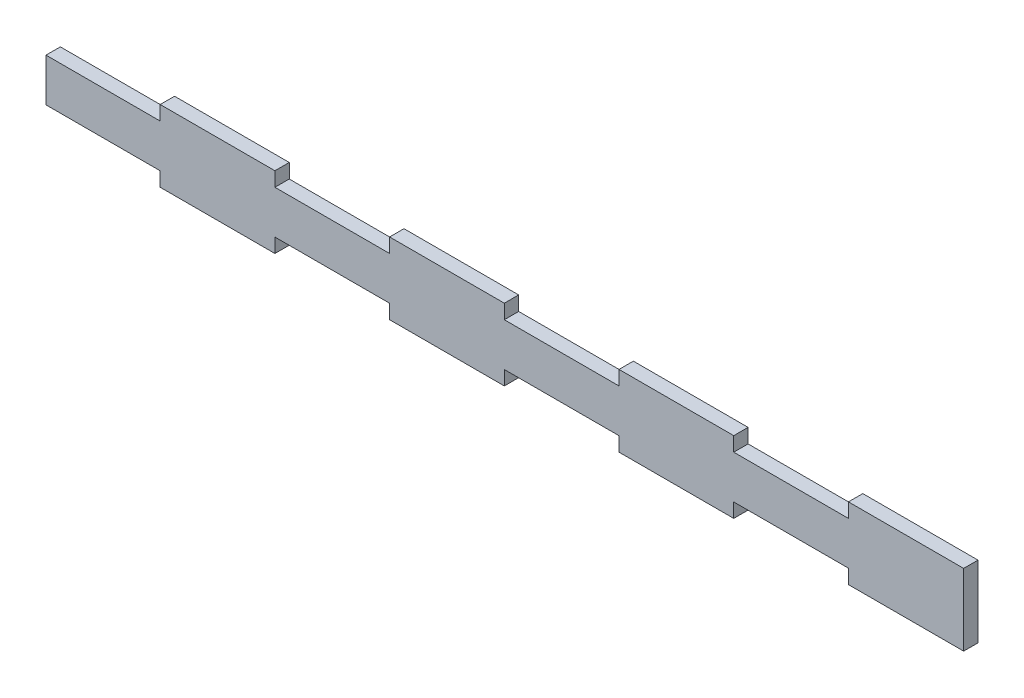
SolidWorks part; units mm, degrees
ref_plane "Front Plane" through (0, 0, 0) normal (0, 0, 1) x (1, 0, 0)
ref_plane "Top Plane" through (0, 0, 0) normal (0, 1, 0) x (1, 0, 0)
ref_plane "Right Plane" through (0, 0, 0) normal (1, 0, 0) x (0, 0, -1)
sketch "Sketch1" plane through (0, 0, 0) normal (0, 0, 1) x (1, 0, 0)
  line L0 (0, 0) -> (101.711, -7.9288) construction
  line L1 (-101.489, -7.9288) -> (101.711, -7.9288)
  line L2 (-101.489, -7.9288) -> (-101.489, 7.9462)
  line L3 (-101.489, 7.9462) -> (101.711, 7.9462)
  line L4 (101.711, -7.9288) -> (101.711, 7.9462)
  line L5 (-101.489, -7.9288) -> (101.711, 7.9462) construction
  line L7 (-101.489, 7.9462) -> (-76.089, 7.9462)
  line L8 (-101.489, 7.9462) -> (-101.489, 6.3587)
  point P0 (0, 0)
  dimension "D1" = 15.875
  dimension "D2" = 203.2
extrude "Boss-Extrude1" add sketch "Sketch1" along normal blind 3.175 contours L3 L4 L1 L2
sketch "Sketch2" plane through (0, 0, 3.175) normal (0, 0, 1) x (1, 0, 0)
  line L0 (-50.8, 7.9462) -> (-50.8, 4.7712)
  line L1 (-101.6, 7.9462) -> (-76.2, 7.9462)
  line L2 (-101.6, 7.9462) -> (-101.6, 4.7712)
  line L3 (-101.6, 4.7712) -> (-76.2, 4.7712)
  line L4 (-76.2, 7.9462) -> (-76.2, 4.7712)
  line L5 (-50.8, 7.9462) -> (-25.4, 7.9462)
  line L6 (-25.4, 7.9462) -> (-25.4, 4.7712)
  line L7 (-50.8, 4.7712) -> (-25.4, 4.7712)
  line L8 (0, 7.9462) -> (0, 4.7712)
  line L9 (0, 7.9462) -> (25.4, 7.9462)
  line L10 (25.4, 7.9462) -> (25.4, 4.7712)
  line L11 (0, 4.7712) -> (25.4, 4.7712)
  line L12 (50.8, 7.9462) -> (50.8, 4.7712)
  line L13 (50.8, 7.9462) -> (76.2, 7.9462)
  line L14 (76.2, 7.9462) -> (76.2, 4.7712)
  line L15 (50.8, 4.7712) -> (76.2, 4.7712)
  line L16 (-101.489, 0) -> (127.7879, 0) construction
  line L18 (50.8, -7.9462) -> (76.2, -7.9462)
  line L19 (76.2, -7.9462) -> (76.2, -4.7712)
  line L20 (50.8, -4.7712) -> (76.2, -4.7712)
  line L21 (50.8, -7.9462) -> (50.8, -4.7712)
  line L22 (0, -7.9462) -> (25.4, -7.9462)
  line L23 (25.4, -7.9462) -> (25.4, -4.7712)
  line L24 (0, -4.7712) -> (25.4, -4.7712)
  line L25 (0, -7.9462) -> (0, -4.7712)
  line L26 (-50.8, -7.9462) -> (-25.4, -7.9462)
  line L27 (-25.4, -7.9462) -> (-25.4, -4.7712)
  line L28 (-50.8, -4.7712) -> (-25.4, -4.7712)
  line L29 (-50.8, -7.9462) -> (-50.8, -4.7712)
  line L30 (-101.6, -4.7712) -> (-76.2, -4.7712)
  line L31 (-76.2, -7.9462) -> (-76.2, -4.7712)
  line L32 (-101.6, -7.9462) -> (-76.2, -7.9462)
  line L33 (-101.6, -7.9462) -> (-101.6, -4.7712)
  line L34 (-101.489, 7.9462) -> (101.711, 7.9462) construction
  dimension "D1" = 3.175
  dimension "D2" = 25.4
  dimension "D3" = 4
extrude "Cut-Extrude1" cut sketch "Sketch2" against normal blind 3.175
